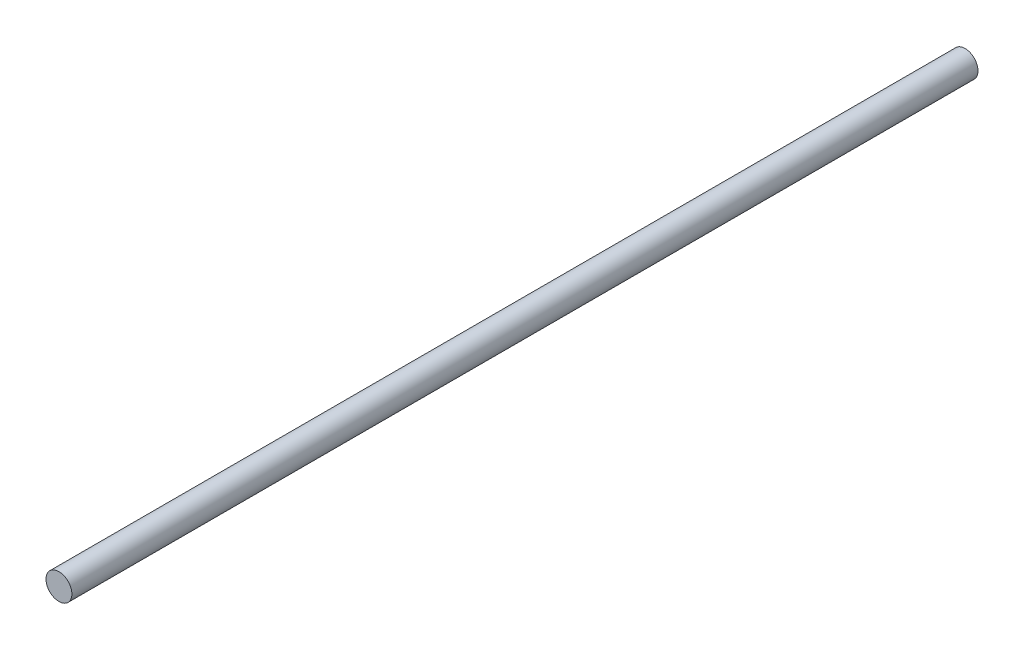
SolidWorks part; units mm, degrees
ref_plane "Plano frontal" through (0, 0, 0) normal (0, 0, 1) x (1, 0, 0)
ref_plane "Plano superior" through (0, 0, 0) normal (0, 1, 0) x (1, 0, 0)
ref_plane "Plano direito" through (0, 0, 0) normal (1, 0, 0) x (0, 0, -1)
sketch "Esboço1" plane through (0, 0, 0) normal (0, 0, 1) x (1, 0, 0)
  circle A0 centre (0, 0) radius 6
  dimension "D1" = 12
extrude "Ressalto-extrusão1" add sketch "Esboço1" along normal blind 420
